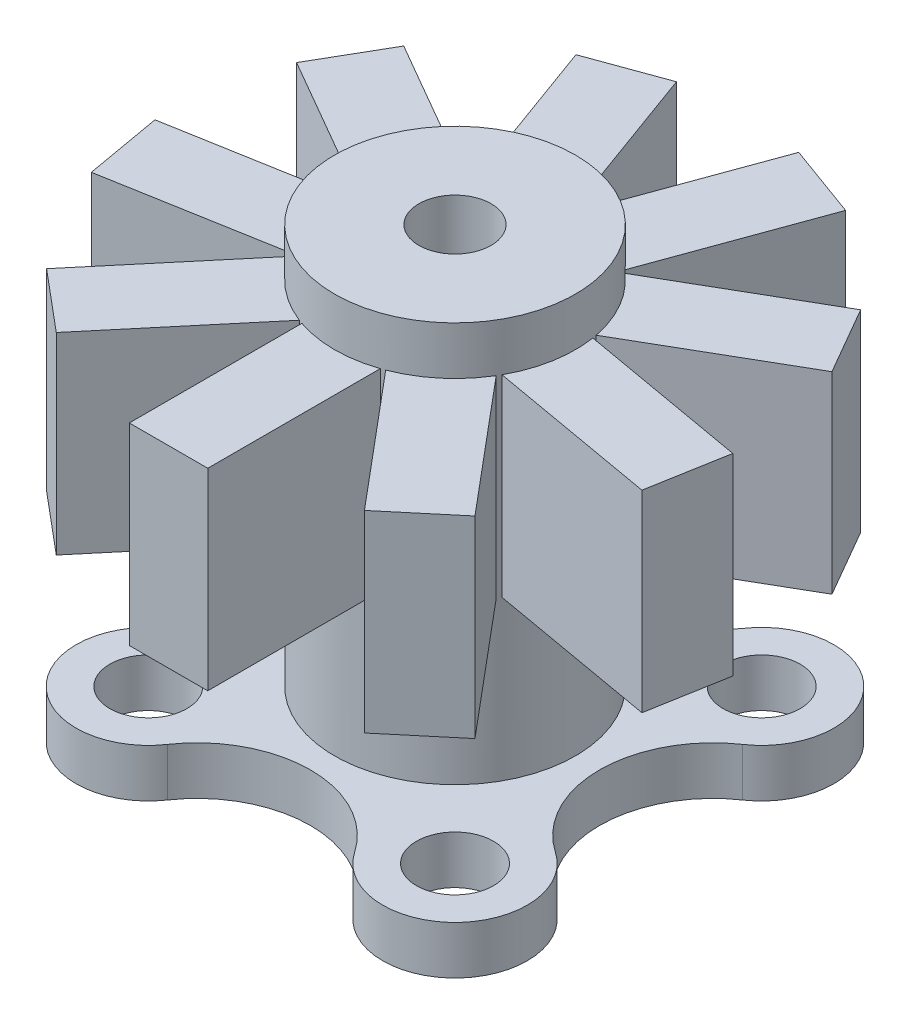
SolidWorks part; units mm, degrees
ref_plane "Front Plane" through (0, 0, 0) normal (0, 0, 1) x (1, 0, 0)
ref_plane "Top Plane" through (0, 0, 0) normal (0, 1, 0) x (1, 0, 0)
ref_plane "Right Plane" through (0, 0, 0) normal (1, 0, 0) x (0, 0, -1)
sketch "Sketch1" plane through (0, 0, 0) normal (0, 1, 0) x (1, 0, 0)
  circle A0 centre (0, 0) radius 2.5
  dimension "D1" = 5
extrude "Boss-Extrude1" add sketch "Sketch1" along normal blind 9.3 contours A0
sketch "Sketch3" plane through (0, 9.3, 0) normal (0, 1, 0) x (1, 0, 0)
  line L0 (0, 0) -> (-0.8139, -2.3638) construction
  line L1 (-0.8139, 0) -> (0.8139, 0)
  line L2 (-0.8139, 0) -> (-0.8139, -5.9445)
  line L3 (-0.8139, -5.9445) -> (0.8139, -5.9445)
  line L4 (0.8139, 0) -> (0.8139, -5.9445)
  line L5 (0, 0) -> (0.8139, -2.3638) construction
  circle A0 centre (0, 0) radius 2.5 construction
  circle A1 centre (0, 0) radius 6 construction
  dimension "D2" = 12
  dimension "D1" = 38
extrude "Boss-Extrude2" add sketch "Sketch3" against normal blind 4 from offset 1 offset against normal yes
pattern_circular "CirPattern1" count 9 over 360 about axis through (0, 0, 0) along (0, 1, 0) of "Boss-Extrude2"
sketch "Sketch4" plane through (0, 0, 0) normal (0, -1, 0) x (1, 0, 0)
  line L0 (0, 0) -> (0, 3) construction
  circle A0 centre (0, 0) radius 3 construction
  arc A1 (-1.9425, 4.0268) -> (-4.0268, 1.9425) centre (-3.182, 3.182) ccw
  circle A2 centre (0, 0) radius 4.5 construction
  arc A3 (4.0268, 1.9425) -> (1.9425, 4.0268) centre (3.182, 3.182) ccw
  arc A4 (1.9425, -4.0268) -> (4.0268, -1.9425) centre (3.182, -3.182) ccw
  arc A5 (-4.0268, -1.9425) -> (-1.9425, -4.0268) centre (-3.182, -3.182) ccw
  arc A6 (-4.0268, -1.9425) -> (-4.0268, 1.9425) centre (-5.3508, 0) ccw
  arc A7 (-1.9425, 4.0268) -> (1.9425, 4.0268) centre (0, 5.3508) ccw
  arc A8 (4.0268, 1.9425) -> (4.0268, -1.9425) centre (5.3508, 0) ccw
  arc A9 (1.9425, -4.0268) -> (-1.9425, -4.0268) centre (0, -5.3508) ccw
  point P15 (0, 0)
  point P28 (0, 0)
  dimension "D1" = 4
  dimension "D2" = 3
  dimension "D3" = 9
  dimension "D4" = 4
extrude "Boss-Extrude3" add sketch "Sketch4" against normal blind 1
hole_wizard "M2x0.4 Tapped Hole1" positions "Sketch5" profile "Sketch6" tap size "M2x0.4" standard "ANSI Metric" end condition up to next
sketch "Sketch5" plane through (0, 0, 0) normal (0, -1, 0) x (-1, 0, 0)
  point P0 (3.182, 3.182)
  point P3 (-3.182, 3.182)
  point P6 (-3.182, -3.182)
  point P9 (3.182, -3.182)
sketch "Sketch6" plane through (-3.182, 0, -3.182) normal (1, 0, 0) x (0, 0, -1)
  line L0 (0, 0) -> (0, 1)
  line L1 (0, 1) -> (0.8, 1)
  line L2 (0.8, 1) -> (0.8, 0)
  line L5 (0.8, 0) -> (0, 0)
  line L11 (0, -6.35) -> (0, 107.95) construction
  dimension "Thru Tap Drill Dia." = 1.6
  dimension "Thru Tap Drill Depth" = 1
cosmetic thread "Hole Thread1" parameters "D2"=2
cosmetic thread "Hole Thread2" parameters "D2"=2
cosmetic thread "Hole Thread3" parameters "D2"=2
cosmetic thread "Hole Thread4" parameters "D2"=2
sketch "Sketch7" plane through (0, 0, 0) normal (0, -1, 0) x (1, 0, 0)
  circle A0 centre (0, 0) radius 0.75
  dimension "D1" = 1.5
extrude "Cut-Extrude1" cut sketch "Sketch7" against normal through all
